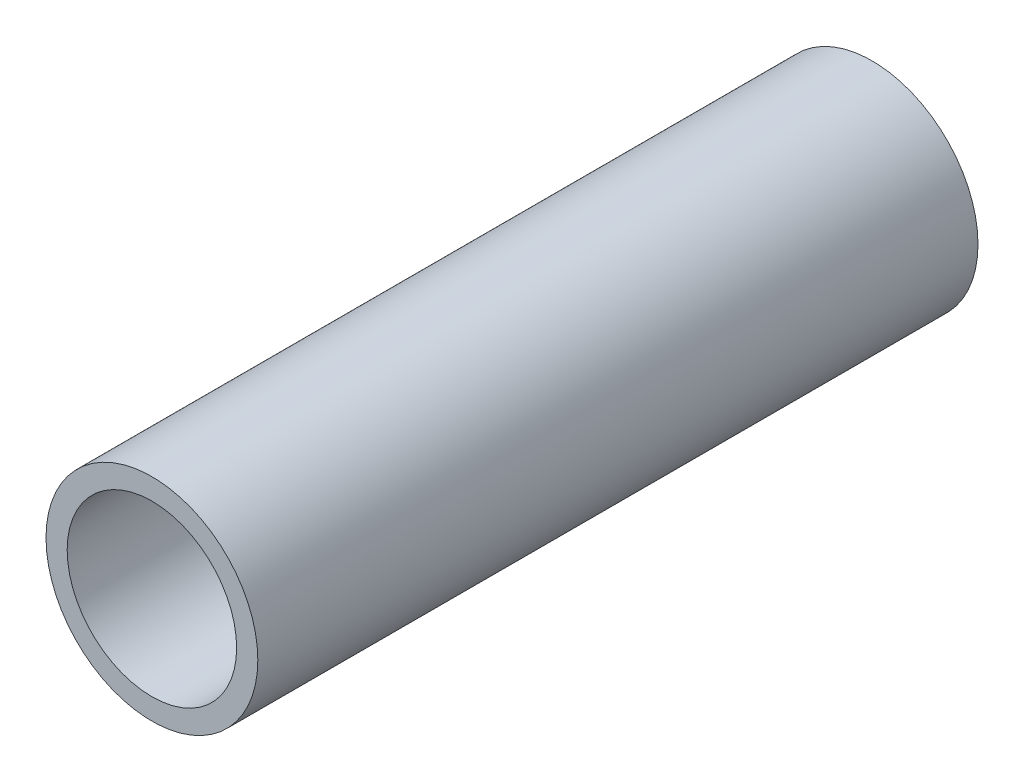
SolidWorks part; units mm, degrees
ref_plane "Front Plane" through (0, 0, 0) normal (0, 0, 1) x (1, 0, 0)
ref_plane "Top Plane" through (0, 0, 0) normal (0, 1, 0) x (1, 0, 0)
ref_plane "Right Plane" through (0, 0, 0) normal (1, 0, 0) x (0, 0, -1)
sketch "Sketch1" plane through (0, 0, 0) normal (0, 0, 1) x (1, 0, 0)
  circle A0 centre (0, 0) radius 1
  circle A1 centre (0, 0) radius 1.25
  dimension "D1" = 2
  dimension "D2" = 2.5
extrude "Tube MCP Body" add sketch "Sketch1" along normal blind 8.5
